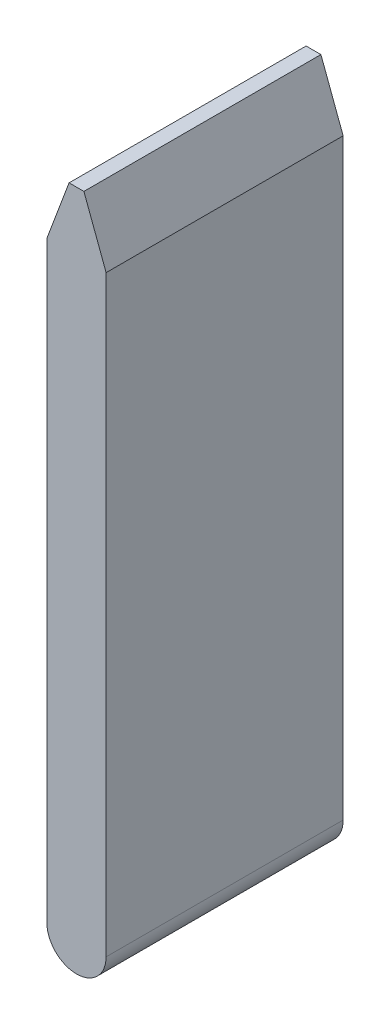
SolidWorks part; units mm, degrees
ref_plane "Front Plane" through (0, 0, 0) normal (0, 0, 1) x (1, 0, 0)
ref_plane "Top Plane" through (0, 0, 0) normal (0, 1, 0) x (1, 0, 0)
ref_plane "Right Plane" through (0, 0, 0) normal (1, 0, 0) x (0, 0, -1)
curve "Curva2"
  spline degree 3 poles (124.9992, -0.7862, 0) (125.0006, 0, 0) (124.9984, 0.7862, 0) (124.9909, 1.5723, 0) (124.9786, 2.3584, 0) (124.9613, 3.1444, 0) (124.939, 3.9303, 0) (124.9118, 4.716, 0) (124.8797, 5.5015, 0) (124.8426, 6.2869, 0) (124.8006, 7.0719, 0) (124.7537, 7.8567, 0) (124.7018, 8.6412, 0) (124.645, 9.4253, 0) (124.5832, 10.2091, 0) (124.5166, 10.9924, 0) (124.445, 11.7754, 0) (124.3684, 12.5578, 0) (124.287, 13.3398, 0) (124.2006, 14.1212, 0) (124.1094, 14.9021, 0) (124.0132, 15.6824, 0) (123.9121, 16.462, 0) (123.8061, 17.241, 0) (123.6952, 18.0194, 0) (123.5794, 18.797, 0) (123.4588, 19.5738, 0) (123.3332, 20.3499, 0) (123.2028, 21.1252, 0) (123.0675, 21.8997, 0) (122.9273, 22.6733, 0) (122.7823, 23.446, 0) (122.6324, 24.2178, 0) (122.4777, 24.9886, 0) (122.3181, 25.7584, 0) (122.1537, 26.5272, 0) (121.9844, 27.2949, 0) (121.8103, 28.0616, 0) (121.6314, 28.8272, 0) (121.4477, 29.5916, 0) (121.2592, 30.3548, 0) (121.0659, 31.1169, 0) (120.8678, 31.8777, 0) (120.6649, 32.6373, 0) (120.4572, 33.3955, 0) (120.2448, 34.1525, 0) (120.0276, 34.9081, 0) (119.8057, 35.6623, 0) (119.579, 36.4151, 0) (119.3476, 37.1665, 0) (119.1115, 37.9164, 0) (118.8707, 38.6648, 0) (118.6252, 39.4116, 0) (118.3749, 40.1569, 0) (118.12, 40.9006, 0) (117.8605, 41.6427, 0) (117.5962, 42.3832, 0) (117.3273, 43.122, 0) (117.0538, 43.859, 0) (116.7756, 44.5944, 0) (116.4928, 45.328, 0) (116.2055, 46.0597, 0) (115.9135, 46.7897, 0) (115.6169, 47.5178, 0) (115.3157, 48.244, 0) (115.01, 48.9683, 0) (114.6998, 49.6907, 0) (114.385, 50.4111, 0) (114.0657, 51.1295, 0) (113.7418, 51.8459, 0) (113.4135, 52.5603, 0) (113.0807, 53.2726, 0) (112.7434, 53.9827, 0) (112.4016, 54.6907, 0) (112.0554, 55.3966, 0) (111.7048, 56.1003, 0) (111.3498, 56.8017, 0) (110.9903, 57.5009, 0) (110.6265, 58.1979, 0) (110.2583, 58.8925, 0) (109.8857, 59.5848, 0) (109.5087, 60.2747, 0) (109.1275, 60.9623, 0) (108.7419, 61.6474, 0) (108.352, 62.3301, 0) (107.9579, 63.0104, 0) (107.5594, 63.6881, 0) (107.1567, 64.3633, 0) (106.7498, 65.036, 0) (106.3387, 65.7061, 0) (105.9233, 66.3736, 0) (105.5038, 67.0385, 0) (105.08, 67.7008, 0) (104.6522, 68.3603, 0) (104.2201, 69.0172, 0) (103.784, 69.6713, 0) (103.3438, 70.3226, 0) (102.8994, 70.9712, 0) (102.451, 71.617, 0) (101.9986, 72.2599, 0) (101.5421, 72.9, 0) (101.0816, 73.5372, 0) (100.6171, 74.1715, 0) (100.1486, 74.8029, 0) (99.6761, 75.4313, 0) (99.1997, 76.0567, 0) (98.7194, 76.6791, 0) (98.2352, 77.2985, 0) (97.7471, 77.9148, 0) (97.2551, 78.528, 0) (96.7593, 79.1381, 0) (96.2596, 79.7451, 0) (95.7562, 80.349, 0) (95.2489, 80.9496, 0) (94.7379, 81.5471, 0) (94.2232, 82.1413, 0) (93.7047, 82.7323, 0) (93.1825, 83.32, 0) (92.6566, 83.9045, 0) (92.1271, 84.4856, 0) (91.5939, 85.0633, 0) (91.0571, 85.6377, 0) (90.5167, 86.2087, 0) (89.9727, 86.7763, 0) (89.4251, 87.3405, 0) (88.874, 87.9012, 0) (88.3194, 88.4584, 0) (87.7613, 89.0121, 0) (87.1997, 89.5623, 0) (86.6347, 90.109, 0) (86.0663, 90.6521, 0) (85.4944, 91.1916, 0) (84.9192, 91.7275, 0) (84.3406, 92.2598, 0) (83.7587, 92.7884, 0) (83.1734, 93.3134, 0) (82.5849, 93.8347, 0) (81.9931, 94.3522, 0) (81.398, 94.866, 0) (80.7998, 95.3761, 0) (80.1983, 95.8824, 0) (79.5937, 96.3849, 0) (78.9859, 96.8836, 0) (78.375, 97.3785, 0) (77.761, 97.8695, 0) (77.1439, 98.3566, 0) (76.5238, 98.8399, 0) (75.9006, 99.3192, 0) (75.2745, 99.7946, 0) (74.6453, 100.2661, 0) (74.0132, 100.7336, 0) (73.3782, 101.1971, 0) (72.7403, 101.6566, 0) (72.0995, 102.1121, 0) (71.4558, 102.5635, 0) (70.8093, 103.0109, 0) (70.1601, 103.4542, 0) (69.508, 103.8934, 0) (68.8532, 104.3285, 0) (68.1957, 104.7595, 0) (67.5354, 105.1864, 0) (66.8725, 105.609, 0) (66.207, 106.0275, 0) (65.5388, 106.4418, 0) (64.8681, 106.8519, 0) (64.1948, 107.2578, 0) (63.5189, 107.6594, 0) (62.8405, 108.0568, 0) (62.1597, 108.4499, 0) (61.4764, 108.8387, 0) (60.7906, 109.2232, 0) (60.1025, 109.6034, 0) (59.4119, 109.9792, 0) (58.719, 110.3507, 0) (58.0238, 110.7178, 0) (57.3263, 111.0806, 0) (56.6266, 111.4389, 0) (55.9246, 111.7929, 0) (55.2203, 112.1424, 0) (54.5139, 112.4875, 0) (53.8054, 112.8281, 0) (53.0947, 113.1643, 0) (52.3819, 113.496, 0) (51.667, 113.8232, 0) (50.9501, 114.1459, 0) (50.2312, 114.4641, 0) (49.5103, 114.7778, 0) (48.7874, 115.0869, 0) (48.0626, 115.3915, 0) (47.3359, 115.6915, 0) (46.6074, 115.9869, 0) (45.877, 116.2777, 0) (45.1447, 116.564, 0) (44.4107, 116.8456, 0) (43.6749, 117.1226, 0) (42.9374, 117.395, 0) (42.1982, 117.6627, 0) (41.4574, 117.9258, 0) (40.7149, 118.1842, 0) (39.9708, 118.4379, 0) (39.2251, 118.687, 0) (38.4778, 118.9313, 0) (37.729, 119.171, 0) (36.9788, 119.4059, 0) (36.227, 119.6361, 0) (35.4739, 119.8616, 0) (34.7193, 120.0824, 0) (33.9634, 120.2984, 0) (33.2061, 120.5096, 0) (32.4475, 120.7161, 0) (31.6876, 120.9177, 0) (30.9265, 121.1146, 0) (30.1641, 121.3068, 0) (29.4006, 121.4941, 0) (28.6359, 121.6766, 0) (27.87, 121.8543, 0) (27.1031, 122.0272, 0) (26.3351, 122.1952, 0) (25.566, 122.3584, 0) (24.796, 122.5168, 0) (24.0249, 122.6703, 0) (23.2529, 122.819, 0) (22.48, 122.9628, 0) (21.7062, 123.1018, 0) (20.9315, 123.2359, 0) (20.156, 123.3651, 0) (19.3797, 123.4894, 0) (18.6026, 123.6088, 0) (17.8248, 123.7234, 0) (17.0463, 123.8331, 0) (16.2672, 123.9378, 0) (15.4873, 124.0377, 0) (14.7069, 124.1326, 0) (13.9259, 124.2227, 0) (13.1443, 124.3078, 0) (12.3622, 124.388, 0) (11.5797, 124.4633, 0) (10.7966, 124.5337, 0) (10.0132, 124.5991, 0) (9.2293, 124.6596, 0) (8.4451, 124.7152, 0) (7.6605, 124.7659, 0) (6.8757, 124.8116, 0) (6.0906, 124.8524, 0) (5.3052, 124.8882, 0) (4.5196, 124.9191, 0) (3.7338, 124.945, 0) (2.9479, 124.9661, 0) (2.1619, 124.9821, 0) (1.3758, 124.9933, 0) (0.5896, 124.9994, 0) (-0.1965, 125.0007, 0) (-0.9827, 124.997, 0) (-1.7689, 124.9883, 0) (-2.5549, 124.9747, 0) (-3.3409, 124.9562, 0) (-4.1267, 124.9327, 0) (-4.9124, 124.9043, 0) (-5.6979, 124.8709, 0) (-6.4832, 124.8326, 0) (-7.2682, 124.7893, 0) (-8.0529, 124.7412, 0) (-8.8373, 124.688, 0) (-9.6213, 124.63, 0) (-10.405, 124.567, 0) (-11.1882, 124.4991, 0) (-11.971, 124.4263, 0) (-12.7533, 124.3485, 0) (-13.5352, 124.2659, 0) (-14.3165, 124.1783, 0) (-15.0972, 124.0858, 0) (-15.8773, 123.9884, 0) (-16.6568, 123.8861, 0) (-17.4357, 123.7788, 0) (-18.2138, 123.6667, 0) (-18.9913, 123.5497, 0) (-19.7679, 123.4279, 0) (-20.5438, 123.3011, 0) (-21.3189, 123.1694, 0) (-22.0932, 123.0329, 0) (-22.8666, 122.8915, 0) (-23.639, 122.7453, 0) (-24.4105, 122.5942, 0) (-25.1811, 122.4382, 0) (-25.9507, 122.2774, 0) (-26.7192, 122.1118, 0) (-27.4867, 121.9413, 0) (-28.2531, 121.766, 0) (-29.0184, 121.5859, 0) (-29.7825, 121.401, 0) (-30.5455, 121.2113, 0) (-31.3072, 121.0168, 0) (-32.0677, 120.8175, 0) (-32.827, 120.6134, 0) (-33.5849, 120.4046, 0) (-34.3415, 120.191, 0) (-35.0968, 119.9726, 0) (-35.8506, 119.7495, 0) (-36.6031, 119.5216, 0) (-37.3541, 119.2891, 0) (-38.1036, 119.0518, 0) (-38.8516, 118.8098, 0) (-39.5981, 118.563, 0) (-40.343, 118.3117, 0) (-41.0863, 118.0556, 0) (-41.828, 117.7948, 0) (-42.5681, 117.5294, 0) (-43.3064, 117.2594, 0) (-44.043, 116.9847, 0) (-44.7779, 116.7054, 0) (-45.5111, 116.4214, 0) (-46.2424, 116.1329, 0) (-46.9719, 115.8398, 0) (-47.6995, 115.542, 0) (-48.4253, 115.2397, 0) (-49.1491, 114.9329, 0) (-49.871, 114.6215, 0) (-50.5909, 114.3056, 0) (-51.3088, 113.9851, 0) (-52.0247, 113.6602, 0) (-52.7385, 113.3307, 0) (-53.4503, 112.9968, 0) (-54.1599, 112.6584, 0) (-54.8674, 112.3155, 0) (-55.5727, 111.9682, 0) (-56.2758, 111.6165, 0) (-56.9767, 111.2603, 0) (-57.6754, 110.8998, 0) (-58.3717, 110.5348, 0) (-59.0658, 110.1655, 0) (-59.7575, 109.7918, 0) (-60.4468, 109.4139, 0) (-61.1337, 109.0314, 0) (-61.8185, 108.6452, 0) (-62.4997, 108.2526, 0) (-63.183, 107.8633, 0) (-63.8743, 107.4871, 0) (-64.5721, 107.1211, 0) (-65.2773, 106.766, 0) (-65.9899, 106.4212, 0) (-66.7101, 106.0868, 0) (-67.4383, 105.7624, 0) (-68.1746, 105.4478, 0) (-68.9192, 105.143, 0) (-69.6724, 104.8475, 0) (-70.4344, 104.5612, 0) (-71.2054, 104.2839, 0) (-71.9855, 104.0153, 0) (-72.775, 103.7552, 0) (-73.574, 103.5032, 0) (-74.3826, 103.2592, 0) (-75.2011, 103.0228, 0) (-76.0296, 102.7937, 0) (-76.8683, 102.5718, 0) (-77.7172, 102.3566, 0) (-78.5766, 102.148, 0) (-79.4464, 101.9455, 0) (-80.327, 101.7489, 0) (-81.2182, 101.5579, 0) (-82.1203, 101.3721, 0) (-83.0333, 101.1912, 0) (-83.9572, 101.0149, 0) (-84.8923, 100.8429, 0) (-85.8384, 100.6748, 0) (-86.7957, 100.5102, 0) (-87.7642, 100.3489, 0) (-88.744, 100.1905, 0) (-89.7349, 100.0347, 0) (-90.7372, 99.881, 0) (-91.7506, 99.7291, 0) (-92.7753, 99.5787, 0) (-93.8113, 99.4295, 0) (-94.8584, 99.2809, 0) (-95.9167, 99.1328, 0) (-96.986, 98.9847, 0) (-98.0665, 98.8362, 0) (-99.1578, 98.6871, 0) (-100.2601, 98.5368, 0) (-101.3732, 98.3851, 0) (-102.497, 98.2316, 0) (-103.6314, 98.0759, 0) (-104.7762, 97.9177, 0) (-105.9314, 97.7565, 0) (-107.0969, 97.5921, 0) (-108.2724, 97.424, 0) (-109.4578, 97.2519, 0) (-110.6529, 97.0755, 0) (-111.8576, 96.8943, 0) (-113.0717, 96.7081, 0) (-114.295, 96.5164, 0) (-115.5272, 96.3189, 0) (-116.7682, 96.1152, 0) (-118.0178, 95.9051, 0) (-119.2757, 95.6882, 0) (-120.5417, 95.4641, 0) (-121.8154, 95.2324, 0) (-123.0968, 94.993, 0) (-124.3855, 94.7454, 0) (-125.6812, 94.4893, 0) (-126.9836, 94.2244, 0) (-128.2925, 93.9503, 0) (-129.6076, 93.6669, 0) (-130.9285, 93.3737, 0) (-132.2549, 93.0705, 0) (-133.5866, 92.757, 0) (-134.9232, 92.4329, 0) (-136.2643, 92.0979, 0) (-137.6096, 91.7517, 0) (-138.9588, 91.3941, 0) (-140.3115, 91.0249, 0) (-141.6674, 90.6437, 0) (-143.026, 90.2503, 0) (-144.3871, 89.8445, 0) (-145.7501, 89.4261, 0) (-147.1148, 88.9948, 0) (-148.4807, 88.5504, 0) (-149.8475, 88.0927, 0) (-151.2147, 87.6215, 0) (-152.582, 87.1366, 0) (-153.9489, 86.6378, 0) (-155.3151, 86.125, 0) (-156.68, 85.598, 0) (-158.0433, 85.0566, 0) (-159.4045, 84.5006, 0) (-160.7633, 83.93, 0) (-162.1191, 83.3446, 0) (-163.4716, 82.7443, 0) (-164.8203, 82.1289, 0) (-166.1648, 81.4984, 0) (-167.5046, 80.8527, 0) (-168.8393, 80.1916, 0) (-170.1684, 79.5151, 0) (-171.4915, 78.8232, 0) (-172.8082, 78.1157, 0) (-174.1179, 77.3926, 0) (-175.4203, 76.654, 0) (-176.7149, 75.8997, 0) (-178.0012, 75.1297, 0) (-179.2788, 74.344, 0) (-180.5472, 73.5427, 0) (-181.806, 72.7257, 0) (-183.0548, 71.8931, 0) (-184.2931, 71.0448, 0) (-185.5204, 70.181, 0) (-186.7363, 69.3016, 0) (-187.9404, 68.4068, 0) (-189.1321, 67.4965, 0) (-190.3112, 66.5709, 0) (-191.4771, 65.6301, 0) (-192.6295, 64.6741, 0) (-193.7678, 63.7031, 0) (-194.8917, 62.7171, 0) (-196.0007, 61.7163, 0) (-197.0944, 60.7009, 0) (-198.1725, 59.6709, 0) (-199.2344, 58.6266, 0) (-200.2799, 57.568, 0) (-201.3084, 56.4954, 0) (-202.3197, 55.4089, 0) (-203.3132, 54.3087, 0) (-204.2887, 53.195, 0) (-205.2458, 52.068, 0) (-206.184, 50.9279, 0) (-207.103, 49.775, 0) (-208.0026, 48.6095, 0) (-208.8822, 47.4315, 0) (-209.7415, 46.2414, 0) (-210.5803, 45.0394, 0) (-211.3982, 43.8258, 0) (-212.1949, 42.6007, 0) (-212.97, 41.3646, 0) (-213.7233, 40.1176, 0) (-214.4544, 38.8601, 0) (-215.1631, 37.5924, 0) (-215.849, 36.3147, 0) (-216.512, 35.0273, 0) (-217.1517, 33.7307, 0) (-217.7678, 32.425, 0) (-218.3602, 31.1106, 0) (-218.9286, 29.7879, 0) (-219.4728, 28.4571, 0) (-219.9925, 27.1186, 0) (-220.4875, 25.7729, 0) (-220.9577, 24.4201, 0) (-221.4028, 23.0606, 0) (-221.8226, 21.6949, 0) (-222.2171, 20.3233, 0) (-222.586, 18.9461, 0) (-222.9292, 17.5637, 0) (-223.2465, 16.1764, 0) (-223.5378, 14.7848, 0) (-223.8031, 13.389, 0) (-224.0421, 11.9896, 0) (-224.2548, 10.5869, 0) (-224.4411, 9.1812, 0) (-224.6009, 7.773, 0) (-224.7342, 6.3627, 0) (-224.8409, 4.9506, 0) (-224.921, 3.5371, 0) (-224.9743, 2.1227, 0) (-225.0014, 0.7076, 0) (-225.0001, -0.7076, 0) (-224.9915, -2.1227, 0) (-224.9737, -3.5377, 0) (-224.947, -4.9526, 0) (-224.9114, -6.3673, 0) (-224.8669, -7.7817, 0) (-224.8135, -9.1959, 0) (-224.7512, -10.6096, 0) (-224.68, -12.023, 0) (-224.6, -13.4358, 0) (-224.511, -14.8482, 0) (-224.4132, -16.2599, 0) (-224.3065, -17.671, 0) (-224.1909, -19.0815, 0) (-224.0665, -20.4911, 0) (-223.9332, -21.9, 0) (-223.791, -23.3079, 0) (-223.64, -24.715, 0) (-223.4801, -26.1211, 0) (-223.3114, -27.5261, 0) (-223.1339, -28.9301, 0) (-222.9475, -30.3329, 0) (-222.7523, -31.7345, 0) (-222.5483, -33.1349, 0) (-222.3355, -34.5339, 0) (-222.1139, -35.9316, 0) (-221.8835, -37.3279, 0) (-221.6444, -38.7226, 0) (-221.3964, -40.1159, 0) (-221.1398, -41.5076, 0) (-220.8743, -42.8976, 0) (-220.6002, -44.2859, 0) (-220.3173, -45.6725, 0) (-220.0256, -47.0572, 0) (-219.7253, -48.4402, 0) (-219.4163, -49.8211, 0) (-219.0986, -51.2002, 0) (-218.7723, -52.5772, 0) (-218.4373, -53.9521, 0) (-218.0936, -55.3248, 0) (-217.7413, -56.6954, 0) (-217.3805, -58.0638, 0) (-217.011, -59.4298, 0) (-216.6329, -60.7935, 0) (-216.2463, -62.1548, 0) (-215.8511, -63.5137, 0) (-215.4473, -64.87, 0) (-215.0351, -66.2238, 0) (-214.6143, -67.5749, 0) (-214.1851, -68.9234, 0) (-213.7473, -70.2691, 0) (-213.3012, -71.6121, 0) (-212.8465, -72.9522, 0) (-212.3835, -74.2894, 0) (-211.9121, -75.6237, 0) (-211.4322, -76.955, 0) (-210.944, -78.2833, 0) (-210.4475, -79.6085, 0) (-209.9427, -80.9305, 0) (-209.4295, -82.2493, 0) (-208.9081, -83.5649, 0) (-208.3784, -84.8771, 0) (-207.8404, -86.186, 0) (-207.2942, -87.4915, 0) (-206.7399, -88.7936, 0) (-206.1773, -90.0921, 0) (-205.6066, -91.3871, 0) (-205.0278, -92.6784, 0) (-204.4408, -93.9661, 0) (-203.8458, -95.25, 0) (-203.2427, -96.5302, 0) (-202.6315, -97.8066, 0) (-202.0124, -99.0791, 0) (-201.3852, -100.3477, 0) (-200.7501, -101.6123, 0) (-200.1071, -102.8729, 0) (-199.4561, -104.1294, 0) (-198.7972, -105.3818, 0) (-198.1305, -106.6301, 0) (-197.456, -107.8741, 0) (-196.7736, -109.1138, 0) (-196.0834, -110.3493, 0) (-195.3854, -111.5803, 0) (-194.6801, -112.8071, 0) (-193.965, -114.0283, 0) (-193.2397, -115.2434, 0) (-192.5044, -116.4525, 0) (-191.7591, -117.6553, 0) (-191.0038, -118.8519, 0) (-190.2387, -120.0421, 0) (-189.4637, -121.2259, 0) (-188.679, -122.4031, 0) (-187.8846, -123.5737, 0) (-187.0806, -124.7375, 0) (-186.2671, -125.8946, 0) (-185.444, -127.0447, 0) (-184.6115, -128.1878, 0) (-183.7697, -129.3239, 0) (-182.9185, -130.4528, 0) (-182.0582, -131.5745, 0) (-181.1886, -132.6888, 0) (-180.31, -133.7957, 0) (-179.4224, -134.8951, 0) (-178.5259, -135.987, 0) (-177.6205, -137.0711, 0) (-176.7063, -138.1476, 0) (-175.7834, -139.2162, 0) (-174.8518, -140.2769, 0) (-173.9117, -141.3297, 0) (-172.9631, -142.3744, 0) (-172.0061, -143.4109, 0) (-171.0408, -144.4393, 0) (-170.0672, -145.4594, 0) (-169.0855, -146.4711, 0) (-168.0957, -147.4744, 0) (-167.0979, -148.4692, 0) (-166.0922, -149.4555, 0) (-165.0786, -150.4331, 0) (-164.0573, -151.402, 0) (-163.0283, -152.3622, 0) (-161.9918, -153.3135, 0) (-160.9477, -154.2559, 0) (-159.8963, -155.1894, 0) (-158.8376, -156.1138, 0) (-157.7716, -157.0291, 0) (-156.6985, -157.9353, 0) (-155.6183, -158.8322, 0) (-154.5312, -159.7199, 0) (-153.4372, -160.5982, 0) (-152.3364, -161.4672, 0) (-151.229, -162.3267, 0) (-150.115, -163.1767, 0) (-148.9944, -164.0171, 0) (-147.8675, -164.8479, 0) (-146.7343, -165.6691, 0) (-145.5948, -166.4806, 0) (-144.4493, -167.2822, 0) (-143.2977, -168.0741, 0) (-142.1402, -168.8561, 0) (-140.9768, -169.6282, 0) (-139.8077, -170.3903, 0) (-138.633, -171.1425, 0) (-137.4528, -171.8846, 0) (-136.2671, -172.6166, 0) (-135.0761, -173.3385, 0) (-133.8798, -174.0502, 0) (-132.6784, -174.7517, 0) (-131.472, -175.4429, 0) (-130.2606, -176.1239, 0) (-129.0444, -176.7946, 0) (-127.8234, -177.4549, 0) (-126.5978, -178.1048, 0) (-125.3677, -178.7443, 0) (-124.1331, -179.3733, 0) (-122.8942, -179.9919, 0) (-121.651, -180.5999, 0) (-120.4037, -181.1974, 0) (-119.1524, -181.7844, 0) (-117.8972, -182.3607, 0) (-116.6382, -182.9265, 0) (-115.3754, -183.4816, 0) (-114.109, -184.026, 0) (-112.8391, -184.5597, 0) (-111.5658, -185.0828, 0) (-110.2891, -185.5951, 0) (-109.0093, -186.0967, 0) (-107.7264, -186.5875, 0) (-106.4405, -187.0676, 0) (-105.1517, -187.5369, 0) (-103.86, -187.9953, 0) (-102.5657, -188.443, 0) (-101.2689, -188.8798, 0) (-99.9695, -189.3058, 0) (-98.6678, -189.721, 0) (-97.3638, -190.1253, 0) (-96.0576, -190.5188, 0) (-94.7494, -190.9014, 0) (-93.4392, -191.2732, 0) (-92.1271, -191.6341, 0) (-90.8133, -191.9841, 0) (-89.4978, -192.3232, 0) (-88.1808, -192.6515, 0) (-86.8624, -192.9689, 0) (-85.5425, -193.2755, 0) (-84.2215, -193.5712, 0) (-82.8993, -193.856, 0) (-81.5761, -194.13, 0) (-80.2519, -194.3932, 0) (-78.9269, -194.6455, 0) (-77.6012, -194.887, 0) (-76.2748, -195.1177, 0) (-74.9479, -195.3376, 0) (-73.6206, -195.5467, 0) (-72.2929, -195.7451, 0) (-70.965, -195.9326, 0) (-69.637, -196.1095, 0) (-68.3089, -196.2756, 0) (-66.9809, -196.431, 0) (-65.6531, -196.5757, 0) (-64.3255, -196.7098, 0) (-62.9983, -196.8332, 0) (-61.6716, -196.946, 0) (-60.3454, -197.0481, 0) (-59.0198, -197.1397, 0) (-57.695, -197.2208, 0) (-56.3711, -197.2913, 0) (-55.0481, -197.3513, 0) (-53.7261, -197.4009, 0) (-52.4052, -197.44, 0) (-51.0855, -197.4687, 0) (-49.7672, -197.4871, 0) (-48.4503, -197.4951, 0) (-47.1348, -197.4927, 0) (-45.821, -197.4801, 0) (-44.5088, -197.4573, 0) (-43.1984, -197.4243, 0) (-41.8899, -197.381, 0) (-40.5833, -197.3277, 0) (-39.2787, -197.2642, 0) (-37.9763, -197.1907, 0) (-36.676, -197.1072, 0) (-35.3781, -197.0137, 0) (-34.0826, -196.9103, 0) (-32.7895, -196.797, 0) (-31.499, -196.6739, 0) (-30.2111, -196.5409, 0) (-28.926, -196.3983, 0) (-27.6436, -196.2459, 0) (-26.3641, -196.0838, 0) (-25.0877, -195.9122, 0) (-23.8142, -195.7309, 0) (-22.5439, -195.5402, 0) (-21.2768, -195.34, 0) (-20.013, -195.1304, 0) (-18.7525, -194.9115, 0) (-17.4955, -194.6832, 0) (-16.242, -194.4457, 0) (-14.9921, -194.199, 0) (-13.7458, -193.9431, 0) (-12.5033, -193.6782, 0) (-11.2647, -193.4043, 0) (-10.0299, -193.1213, 0) (-8.799, -192.8295, 0) (-7.5722, -192.5288, 0) (-6.3495, -192.2193, 0) (-5.1309, -191.9011, 0) (-3.9166, -191.5742, 0) (-2.7066, -191.2386, 0) (-1.501, -190.8946, 0) (-0.2998, -190.542, 0) (0.8969, -190.181, 0) (2.0891, -189.8116, 0) (3.2766, -189.434, 0) (4.4595, -189.048, 0) (5.6375, -188.654, 0) (6.8108, -188.2518, 0) (7.9792, -187.8415, 0) (9.1427, -187.4233, 0) (10.3012, -186.9972, 0) (11.4547, -186.5633, 0) (12.603, -186.1215, 0) (13.7463, -185.6721, 0) (14.8843, -185.215, 0) (16.017, -184.7503, 0) (17.1445, -184.2782, 0) (18.2665, -183.7986, 0) (19.3832, -183.3117, 0) (20.4944, -182.8175, 0) (21.6001, -182.316, 0) (22.7003, -181.8074, 0) (23.7948, -181.2917, 0) (24.8837, -180.7691, 0) (25.9669, -180.2395, 0) (27.0444, -179.703, 0) (28.116, -179.1597, 0) (29.1819, -178.6098, 0) (30.2419, -178.0531, 0) (31.296, -177.49, 0) (32.3442, -176.9203, 0) (33.3864, -176.3442, 0) (34.4226, -175.7618, 0) (35.4527, -175.173, 0) (36.4768, -174.5781, 0) (37.4947, -173.9771, 0) (38.5065, -173.37, 0) (39.512, -172.757, 0) (40.5114, -172.138, 0) (41.5046, -171.5132, 0) (42.4914, -170.8827, 0) (43.472, -170.2465, 0) (44.4462, -169.6047, 0) (45.4141, -168.9573, 0) (46.3756, -168.3046, 0) (47.3307, -167.6464, 0) (48.2794, -166.983, 0) (49.2216, -166.3143, 0) (50.1573, -165.6405, 0) (51.0866, -164.9616, 0) (52.0093, -164.2777, 0) (52.9255, -163.5889, 0) (53.8352, -162.8952, 0) (54.7383, -162.1968, 0) (55.6348, -161.4937, 0) (56.5247, -160.7859, 0) (57.408, -160.0736, 0) (58.2847, -159.3568, 0) (59.1548, -158.6357, 0) (60.0182, -157.9102, 0) (60.875, -157.1805, 0) (61.7251, -156.4465, 0) (62.5685, -155.7085, 0) (63.4052, -154.9665, 0) (64.2353, -154.2205, 0) (65.0586, -153.4706, 0) (65.8753, -152.7169, 0) (66.6852, -151.9595, 0) (67.4885, -151.1984, 0) (68.285, -150.4337, 0) (69.0749, -149.6655, 0) (69.858, -148.8939, 0) (70.6344, -148.1189, 0) (71.4041, -147.3406, 0) (72.1671, -146.559, 0) (72.9234, -145.7743, 0) (73.673, -144.9865, 0) (74.4159, -144.1956, 0) (75.1521, -143.4019, 0) (75.8816, -142.6052, 0) (76.6045, -141.8057, 0) (77.3207, -141.0035, 0) (78.0302, -140.1985, 0) (78.733, -139.391, 0) (79.4293, -138.5809, 0) (80.1189, -137.7684, 0) (80.8018, -136.9534, 0) (81.4782, -136.1361, 0) (82.148, -135.3165, 0) (82.8112, -134.4947, 0) (83.4678, -133.6707, 0) (84.1179, -132.8446, 0) (84.7614, -132.0165, 0) (85.3984, -131.1865, 0) (86.029, -130.3545, 0) (86.653, -129.5207, 0) (87.2706, -128.6852, 0) (87.8817, -127.8479, 0) (88.4864, -127.0089, 0) (89.0847, -126.1684, 0) (89.6766, -125.3263, 0) (90.2622, -124.4827, 0) (90.8414, -123.6377, 0) (91.4143, -122.7914, 0) (91.9809, -121.9437, 0) (92.5412, -121.0948, 0) (93.0953, -120.2447, 0) (93.6432, -119.3935, 0) (94.1849, -118.5411, 0) (94.7204, -117.6878, 0) (95.2497, -116.8334, 0) (95.773, -115.9782, 0) (96.2902, -115.122, 0) (96.8013, -114.265, 0) (97.3064, -113.4073, 0) (97.8055, -112.5488, 0) (98.2986, -111.6897, 0) (98.7858, -110.8299, 0) (99.2671, -109.9695, 0) (99.7426, -109.1086, 0) (100.2121, -108.2473, 0) (100.6759, -107.3854, 0) (101.1339, -106.5232, 0) (101.5861, -105.6607, 0) (102.0327, -104.7978, 0) (102.4735, -103.9347, 0) (102.9087, -103.0714, 0) (103.3383, -102.2078, 0) (103.7624, -101.3442, 0) (104.1809, -100.4804, 0) (104.5939, -99.6166, 0) (105.0014, -98.7528, 0) (105.4035, -97.8889, 0) (105.8002, -97.0252, 0) (106.1915, -96.1615, 0) (106.5775, -95.298, 0) (106.9582, -94.4346, 0) (107.3337, -93.5714, 0) (107.704, -92.7084, 0) (108.069, -91.8458, 0) (108.429, -90.9834, 0) (108.7839, -90.1213, 0) (109.1337, -89.2596, 0) (109.4785, -88.3983, 0) (109.8183, -87.5374, 0) (110.1531, -86.677, 0) (110.4831, -85.817, 0) (110.8082, -84.9575, 0) (111.1284, -84.0986, 0) (111.4439, -83.2402, 0) (111.7546, -82.3824, 0) (112.0606, -81.5252, 0) (112.362, -80.6686, 0) (112.6587, -79.8126, 0) (112.9509, -78.9574, 0) (113.2385, -78.1028, 0) (113.5215, -77.2489, 0) (113.8001, -76.3958, 0) (114.0743, -75.5434, 0) (114.3441, -74.6918, 0) (114.6095, -73.841, 0) (114.8706, -72.9909, 0) (115.1275, -72.1417, 0) (115.3801, -71.2933, 0) (115.6285, -70.4458, 0) (115.8728, -69.5991, 0) (116.1129, -68.7534, 0) (116.349, -67.9084, 0) (116.581, -67.0644, 0) (116.8091, -66.2213, 0) (117.0331, -65.3792, 0) (117.2533, -64.5379, 0) (117.4695, -63.6976, 0) (117.682, -62.8582, 0) (117.8906, -62.0198, 0) (118.0954, -61.1824, 0) (118.2965, -60.3459, 0) (118.4939, -59.5104, 0) (118.6877, -58.6759, 0) (118.8778, -57.8423, 0) (119.0644, -57.0098, 0) (119.2474, -56.1782, 0) (119.4269, -55.3476, 0) (119.6029, -54.518, 0) (119.7755, -53.6894, 0) (119.9447, -52.8618, 0) (120.1105, -52.0352, 0) (120.2729, -51.2096, 0) (120.4321, -50.385, 0) (120.588, -49.5613, 0) (120.7407, -48.7387, 0) (120.8901, -47.917, 0) (121.0364, -47.0963, 0) (121.1796, -46.2766, 0) (121.3196, -45.4578, 0) (121.4566, -44.6401, 0) (121.5906, -43.8232, 0) (121.7216, -43.0074, 0) (121.8495, -42.1924, 0) (121.9746, -41.3784, 0) (122.0967, -40.5654, 0) (122.2159, -39.7532, 0) (122.3323, -38.942, 0) (122.4458, -38.1316, 0) (122.5565, -37.3222, 0) (122.6645, -36.5136, 0) (122.7697, -35.7059, 0) (122.8722, -34.8991, 0) (122.972, -34.0931, 0) (123.0691, -33.2879, 0) (123.1636, -32.4835, 0) (123.2555, -31.68, 0) (123.3448, -30.8772, 0) (123.4315, -30.0753, 0) (123.5157, -29.274, 0) (123.5973, -28.4736, 0) (123.6765, -27.6738, 0) (123.7531, -26.8748, 0) (123.8273, -26.0765, 0) (123.8991, -25.2788, 0) (123.9684, -24.4818, 0) (124.0354, -23.6855, 0) (124.1, -22.8898, 0) (124.1622, -22.0947, 0) (124.222, -21.3002, 0) (124.2796, -20.5063, 0) (124.3348, -19.7129, 0) (124.3877, -18.9201, 0) (124.4384, -18.1278, 0) (124.4867, -17.336, 0) (124.5329, -16.5447, 0) (124.5768, -15.7538, 0) (124.6184, -14.9634, 0) (124.6579, -14.1733, 0) (124.6952, -13.3837, 0) (124.7302, -12.5945, 0) (124.7631, -11.8056, 0) (124.7939, -11.017, 0) (124.8224, -10.2288, 0) (124.8488, -9.4408, 0) (124.8731, -8.6531, 0) (124.8953, -7.8657, 0) (124.9153, -7.0785, 0) (124.9332, -6.2915, 0) (124.9489, -5.5047, 0) (124.9626, -4.718, 0) (124.9741, -3.9314, 0) (124.9836, -3.145, 0) (124.9909, -2.3587, 0) (124.9962, -1.5724, 0) (124.9992, -0.7862, 0) (125.0006, 0, 0) (124.9984, 0.7862, 0) knots -0.002215 -0.001476 -0.000738 0 0.000738 0.001476 0.002215 0.002953 0.003691 0.004429 0.005168 0.005906 0.006644 0.007382 0.00812 0.008859 0.009597 0.010335 0.011073 0.011812 0.01255 0.013288 0.014026 0.014764 0.015503 0.016241 0.016979 0.017717 0.018456 0.019194 0.019932 0.02067 0.021409 0.022147 0.022885 0.023623 0.024361 0.0251 0.025838 0.026576 0.027314 0.028053 0.028791 0.029529 0.030267 0.031005 0.031744 0.032482 0.03322 0.033958 0.034697 0.035435 0.036173 0.036911 0.037649 0.038388 0.039126 0.039864 0.040602 0.041341 0.042079 0.042817 0.043555 0.044293 0.045032 0.04577 0.046508 0.047246 0.047985 0.048723 0.049461 0.050199 0.050937 0.051676 0.052414 0.053152 0.05389 0.054629 0.055367 0.056105 0.056843 0.057581 0.05832 0.059058 0.059796 0.060534 0.061273 0.062011 0.062749 0.063487 0.064226 0.064964 0.065702 0.06644 0.067178 0.067917 0.068655 0.069393 0.070131 0.07087 0.071608 0.072346 0.073084 0.073822 0.074561 0.075299 0.076037 0.076775 0.077514 0.078252 0.07899 0.079728 0.080466 0.081205 0.081943 0.082681 0.083419 0.084158 0.084896 0.085634 0.086372 0.08711 0.087849 0.088587 0.089325 0.090063 0.090802 0.09154 0.092278 0.093016 0.093754 0.094493 0.095231 0.095969 0.096707 0.097446 0.098184 0.098922 0.09966 0.100398 0.101137 0.101875 0.102613 0.103351 0.10409 0.104828 0.105566 0.106304 0.107043 0.107781 0.108519 0.109257 0.109995 0.110734 0.111472 0.11221 0.112948 0.113687 0.114425 0.115163 0.115901 0.116639 0.117378 0.118116 0.118854 0.119592 0.120331 0.121069 0.121807 0.122545 0.123283 0.124022 0.12476 0.125498 0.126236 0.126975 0.127713 0.128451 0.129189 0.129927 0.130666 0.131404 0.132142 0.13288 0.133619 0.134357 0.135095 0.135833 0.136571 0.13731 0.138048 0.138786 0.139524 0.140263 0.141001 0.141739 0.142477 0.143215 0.143954 0.144692 0.14543 0.146168 0.146907 0.147645 0.148383 0.149121 0.14986 0.150598 0.151336 0.152074 0.152812 0.153551 0.154289 0.155027 0.155765 0.156504 0.157242 0.15798 0.158718 0.159456 0.160195 0.160933 0.161671 0.162409 0.163148 0.163886 0.164624 0.165362 0.1661 0.166839 0.167577 0.168315 0.169053 0.169792 0.17053 0.171268 0.172006 0.172744 0.173483 0.174221 0.174959 0.175697 0.176436 0.177174 0.177912 0.17865 0.179388 0.180127 0.180865 0.181603 0.182341 0.18308 0.183818 0.184556 0.185294 0.186032 0.186771 0.187509 0.188247 0.188985 0.189724 0.190462 0.1912 0.191938 0.192677 0.193415 0.194153 0.194891 0.195629 0.196368 0.197106 0.197844 0.198582 0.199321 0.200059 0.200797 0.201535 0.202273 0.203012 0.20375 0.204488 0.205226 0.205965 0.206703 0.207441 0.208179 0.208917 0.209656 0.210394 0.211132 0.21187 0.212609 0.213347 0.214085 0.214823 0.215561 0.2163 0.217038 0.217776 0.218514 0.219253 0.219991 0.220729 0.221467 0.222205 0.222944 0.223682 0.22442 0.225158 0.225897 0.226635 0.227373 0.228111 0.228849 0.229588 0.230326 0.231064 0.231802 0.232541 0.233279 0.234017 0.234755 0.235494 0.236232 0.23697 0.237708 0.238446 0.239185 0.239923 0.240661 0.241399 0.242138 0.242876 0.243614 0.244352 0.24509 0.245829 0.246567 0.247306 0.248045 0.248787 0.24953 0.250275 0.251024 0.251775 0.252531 0.25329 0.254054 0.254824 0.255598 0.256379 0.257165 0.257958 0.258758 0.259565 0.260379 0.261202 0.262032 0.262871 0.263718 0.264573 0.265438 0.266312 0.267195 0.268088 0.26899 0.269902 0.270824 0.271756 0.272698 0.27365 0.274612 0.275585 0.276568 0.277561 0.278564 0.279578 0.280602 0.281636 0.282681 0.283736 0.284801 0.285876 0.286961 0.288056 0.289162 0.290277 0.291401 0.292536 0.29368 0.294833 0.295996 0.297168 0.298349 0.299539 0.300737 0.301945 0.30316 0.304384 0.305617 0.306857 0.308105 0.309361 0.310624 0.311895 0.313172 0.314457 0.315748 0.317046 0.318351 0.319662 0.320978 0.322301 0.323629 0.324963 0.326302 0.327646 0.328994 0.330348 0.331706 0.333068 0.334434 0.335805 0.337179 0.338556 0.339937 0.341321 0.342707 0.344097 0.345489 0.346883 0.34828 0.349679 0.351079 0.352481 0.353885 0.35529 0.356695 0.358102 0.35951 0.360918 0.362327 0.363737 0.365146 0.366555 0.367965 0.369374 0.370782 0.37219 0.373598 0.375005 0.376411 0.377816 0.379219 0.380622 0.382023 0.383423 0.384822 0.386219 0.387614 0.389008 0.3904 0.39179 0.393179 0.394565 0.395949 0.397332 0.398712 0.400091 0.401467 0.402841 0.404213 0.405583 0.406951 0.408317 0.40968 0.411042 0.412402 0.413759 0.415115 0.416469 0.41782 0.41917 0.420518 0.421865 0.42321 0.424553 0.425894 0.427234 0.428573 0.42991 0.431246 0.432581 0.433915 0.435248 0.43658 0.437912 0.439242 0.440573 0.441902 0.443231 0.44456 0.445889 0.447218 0.448547 0.449876 0.451205 0.452533 0.453862 0.455191 0.45652 0.457849 0.459177 0.460506 0.461835 0.463164 0.464493 0.465821 0.46715 0.468479 0.469808 0.471137 0.472465 0.473794 0.475123 0.476452 0.477781 0.479109 0.480438 0.481767 0.483096 0.484425 0.485753 0.487082 0.488411 0.48974 0.491069 0.492397 0.493726 0.495055 0.496384 0.497713 0.499041 0.50037 0.501699 0.503028 0.504357 0.505685 0.507014 0.508343 0.509672 0.511001 0.512329 0.513658 0.514987 0.516316 0.517645 0.518973 0.520302 0.521631 0.52296 0.524289 0.525618 0.526946 0.528275 0.529604 0.530933 0.532262 0.53359 0.534919 0.536248 0.537577 0.538906 0.540234 0.541563 0.542892 0.544221 0.54555 0.546878 0.548207 0.549536 0.550865 0.552194 0.553522 0.554851 0.55618 0.557509 0.558838 0.560166 0.561495 0.562824 0.564153 0.565481 0.56681 0.568138 0.569466 0.570795 0.572123 0.573451 0.574779 0.576106 0.577434 0.578761 0.580089 0.581416 0.582742 0.584069 0.585395 0.586721 0.588047 0.589373 0.590698 0.592023 0.593348 0.594672 0.595996 0.59732 0.598643 0.599967 0.601289 0.602611 0.603933 0.605255 0.606576 0.607897 0.609217 0.610537 0.611856 0.613175 0.614493 0.615811 0.617128 0.618445 0.619762 0.621077 0.622393 0.623707 0.625021 0.626335 0.627648 0.62896 0.630272 0.631583 0.632893 0.634203 0.635512 0.63682 0.638128 0.639435 0.640742 0.642047 0.643352 0.644656 0.64596 0.647262 0.648564 0.649865 0.651165 0.652465 0.653764 0.655061 0.656358 0.657654 0.65895 0.660244 0.661537 0.66283 0.664122 0.665412 0.666702 0.667991 0.669279 0.670566 0.671852 0.673137 0.674421 0.675704 0.676986 0.678267 0.679547 0.680825 0.682103 0.68338 0.684656 0.68593 0.687203 0.688476 0.689747 0.691017 0.692286 0.693553 0.69482 0.696085 0.697349 0.698612 0.699874 0.701135 0.702394 0.703652 0.704909 0.706164 0.707418 0.708671 0.709923 0.711173 0.712422 0.71367 0.714916 0.716161 0.717405 0.718647 0.719888 0.721127 0.722365 0.723602 0.724837 0.726071 0.727303 0.728534 0.729763 0.730991 0.732217 0.733442 0.734666 0.735888 0.737108 0.738327 0.739544 0.74076 0.741974 0.743187 0.744398 0.745607 0.746815 0.748021 0.749226 0.750429 0.75163 0.752829 0.754027 0.755224 0.756418 0.757611 0.758803 0.759992 0.76118 0.762366 0.76355 0.764733 0.765914 0.767093 0.76827 0.769445 0.770619 0.771791 0.772961 0.774129 0.775296 0.776461 0.777623 0.778784 0.779943 0.781101 0.782256 0.783409 0.784561 0.785711 0.786858 0.788004 0.789148 0.79029 0.79143 0.792568 0.793704 0.794838 0.795971 0.797101 0.798229 0.799355 0.800479 0.801602 0.802722 0.80384 0.804956 0.80607 0.807182 0.808292 0.8094 0.810506 0.81161 0.812712 0.813811 0.814909 0.816004 0.817098 0.818189 0.819278 0.820365 0.82145 0.822533 0.823613 0.824692 0.825768 0.826842 0.827914 0.828984 0.830052 0.831117 0.832181 0.833242 0.834301 0.835358 0.836412 0.837464 0.838515 0.839563 0.840608 0.841652 0.842693 0.843732 0.844769 0.845803 0.846836 0.847866 0.848894 0.849919 0.850943 0.851964 0.852983 0.853999 0.855014 0.856026 0.857035 0.858043 0.859048 0.860051 0.861052 0.86205 0.863047 0.86404 0.865032 0.866021 0.867008 0.867993 0.868976 0.869956 0.870934 0.871909 0.872883 0.873854 0.874823 0.875789 0.876753 0.877715 0.878675 0.879632 0.880587 0.88154 0.882491 0.883439 0.884385 0.885329 0.88627 0.88721 0.888147 0.889081 0.890014 0.890944 0.891872 0.892797 0.893721 0.894642 0.895561 0.896478 0.897392 0.898305 0.899215 0.900123 0.901028 0.901932 0.902833 0.903732 0.904629 0.905523 0.906416 0.907306 0.908195 0.909081 0.909964 0.910846 0.911726 0.912603 0.913479 0.914352 0.915223 0.916092 0.916959 0.917824 0.918687 0.919548 0.920406 0.921263 0.922118 0.92297 0.923821 0.92467 0.925516 0.926361 0.927204 0.928044 0.928883 0.92972 0.930555 0.931388 0.932219 0.933049 0.933876 0.934702 0.935525 0.936347 0.937167 0.937986 0.938802 0.939617 0.94043 0.941241 0.942051 0.942859 0.943665 0.944469 0.945272 0.946073 0.946873 0.947671 0.948467 0.949262 0.950055 0.950847 0.951637 0.952425 0.953212 0.953998 0.954782 0.955565 0.956346 0.957126 0.957905 0.958682 0.959458 0.960233 0.961006 0.961778 0.962549 0.963318 0.964087 0.964854 0.96562 0.966385 0.967148 0.967911 0.968672 0.969433 0.970192 0.970951 0.971708 0.972465 0.97322 0.973975 0.974729 0.975481 0.976233 0.976985 0.977735 0.978485 0.979233 0.979982 0.980729 0.981476 0.982222 0.982967 0.983712 0.984457 0.9852 0.985944 0.986686 0.987429 0.98817 0.988912 0.989653 0.990393 0.991134 0.991874 0.992613 0.993353 0.994092 0.994831 0.99557 0.996308 0.997047 0.997785 0.998524 0.999262 1 1.000738 1.001476 1.002215 periodic
sketch "Croquis1" plane through (0, 0, 0) normal (0, 0, 1) x (1, 0, 0)
  line L0 (-25, 43.3013) -> (25, 43.3013)
  line L1 (-25, 43.3013) -> (-25, 63.3013)
  line L2 (-25, 63.3013) -> (25, 63.3013)
  line L3 (25, 63.3013) -> (25, 43.3013)
  circle A0 centre (0, 0) radius 50
  spline S0 degree 3 number of poles 1002 (125, 0) -> (125, 0) construction
  spline S1 degree 3 number of poles 1002 (125, 0) -> (125, 0)
  dimension "D1" = 100
  dimension "D2" = 50
  dimension "D3" = 20
sketch "Croquis2" plane through (0, 0, 0) normal (0, 0, 1) x (1, 0, 0)
  line L0 (25, 63.3013) -> (25, 43.3013) construction
  line L1 (-25, 63.3013) -> (25, 63.3013) construction
  line L2 (-25, 43.3013) -> (-25, 63.3013) construction
  line L3 (25, 63.3013) -> (25, 43.3013)
  line L4 (-25, 63.3013) -> (25, 63.3013)
  line L5 (-25, 43.3013) -> (-25, 63.3013)
  circle A0 centre (0, 0) radius 50 construction
  arc A1 (-25, 43.3013) -> (25, 43.3013) centre (0, 0) ccw
  spline S0 degree 3 number of poles 1002 (125, 0) -> (125, 0) construction
  spline S1 degree 3 number of poles 1002 (125, 0) -> (125, 0)
extrude "Saliente-Extruir1" [suppressed] add sketch "Croquis2" along normal mid plane 80
sketch "Croquis3" plane through (0, 0, 0) normal (0, 0, 1) x (1, 0, 0)
  line L0 (25, 63.3013) -> (25, 43.3013) construction
  line L1 (-25, 63.3013) -> (25, 63.3013) construction
  line L2 (-25, 43.3013) -> (-25, 63.3013) construction
  line L3 (25, 63.3013) -> (25, 43.3013)
  line L4 (-25, 63.3013) -> (25, 63.3013)
  line L5 (-25, 43.3013) -> (-25, 63.3013)
  circle A0 centre (0, 0) radius 50 construction
  circle A1 centre (0, 0) radius 50
extrude "Saliente-Extruir2" [suppressed] add sketch "Croquis3" against normal blind 80 contours A1 L3 L4 L5 | A1
sketch "Croquis4" plane through (0, 0, 0) normal (0, 0, 1) x (1, 0, 0)
  circle A0 centre (0, 0) radius 50 construction
  circle A1 centre (0, 0) radius 50
extrude "Saliente-Extruir3" [suppressed] add sketch "Croquis4" along normal blind 400
sketch "Croquis5" plane through (0, 0, 0) normal (0, 0, 1) x (1, 0, 0)
  line L0 (-150, 0) -> (-150, -300)
  line L1 (-150, -300) -> (150, -300)
  line L2 (150, -300) -> (150, 0)
  line L3 (0, 0) -> (0, 443.4729) construction
  circle A0 centre (0, 0) radius 50 construction
  circle A1 centre (0, 0) radius 50
  circle A2 centre (0, 0) radius 150
  dimension "D1" = 300
  dimension "D2" = 300
extrude "Saliente-Extruir4" [suppressed] add sketch "Croquis5" along normal mid plane 80 contours A2 A1 | A2 L0 L1 L2
sketch "Croquis6" plane through (0, 0, 0) normal (0, 0, 1) x (1, 0, 0)
  line L0 (-10, 0) -> (-10, 200)
  line L1 (-10, 200) -> (-2.5, 220)
  line L2 (-2.5, 220) -> (2.5, 220)
  line L3 (2.5, 220) -> (10, 200)
  line L4 (10, 200) -> (10, 0)
  line L5 (10, 200) -> (-10, 200) construction
  line L6 (0, 0) -> (0, 200) construction
  circle A0 centre (0, 0) radius 10
  dimension "D1" = 20
  dimension "D2" = 200
  dimension "D3" = 5
  dimension "D4" = 20
extrude "Saliente-Extruir5" add sketch "Croquis6" along normal blind 80 contours L4 L5 L0 A0 | A0 | L5 L3 L2 L1
equation "\"D2@Croquis1\"=\"D1@Croquis1\"/2"
equation "\"D3@Croquis1\"=\"D1@Croquis1\"/5"
equation "\"D1@Croquis5\"=300"
